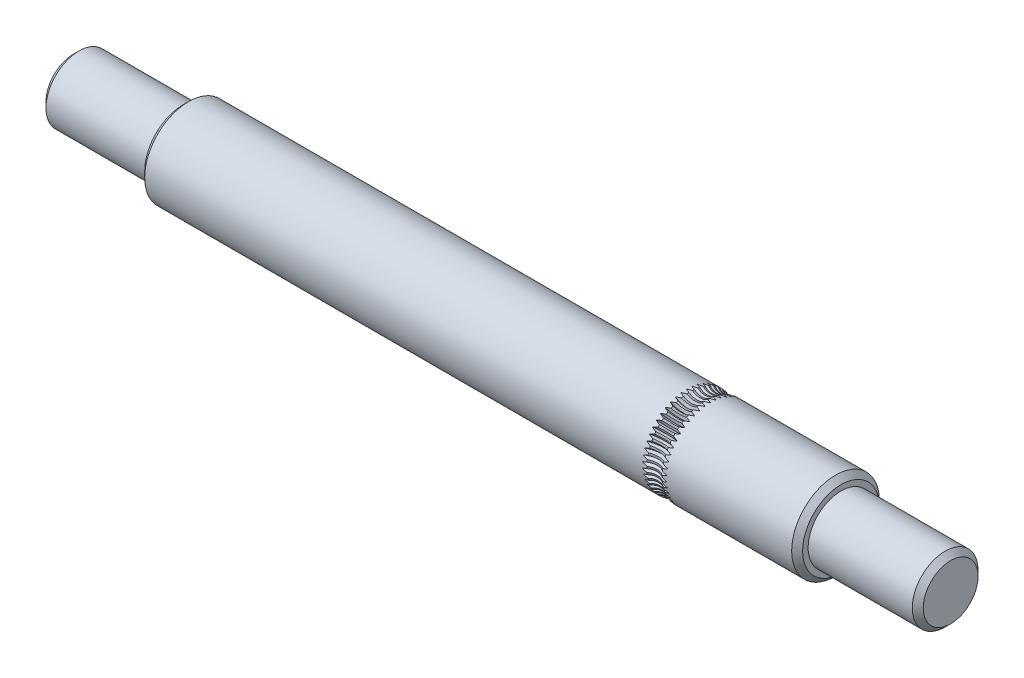
SolidWorks part; units mm, degrees
material "Plain Carbon Steel"
ref_plane "Front Plane" through (0, 0, 0) normal (0, 0, 1) x (1, 0, 0)
ref_plane "Top Plane" through (0, 0, 0) normal (0, 1, 0) x (1, 0, 0)
ref_plane "Right Plane" through (0, 0, 0) normal (1, 0, 0) x (0, 0, -1)
sketch "Sketch1" plane through (0, 0, 0) normal (0, 0, 1) x (1, 0, 0)
  line L0 (-47, 4) -> (13, 4)
  line L1 (-47, 3) -> (-57, 3)
  line L2 (-57, 0) -> (23, 0)
  line L3 (-47, 3) -> (-47, 4)
  line L4 (-57, 3) -> (-57, 0)
  line L5 (23, 0) -> (23, 3)
  line L6 (13, 4) -> (13, 3)
  line L7 (13, 3) -> (23, 3)
  line L8 (0, 0) -> (67.2135, 0) construction
  line L9 (0, 0) -> (0, 19.6593) construction
  dimension "D1" = 8
  dimension "D2" = 60
  dimension "D3" = 13
  dimension "D4" = 10
  dimension "D5" = 6
  dimension "D6" = 10
revolve "Revolve1" add sketch "Sketch1" angle 360 about L8
chamfer "Chamfer1" distance 0.5 angle 45 4 edges at (23, 0, 3) (13, 0, 4) (-47, 0, 4) (-57, 0, 3)
sketch "Sketch2" plane through (0, 0, 0) normal (1, 0, 0) x (0, 0, -1)
  line L0 (0, 0) -> (0, 5) construction
  line L1 (9.9899, 5) -> (-9.864, 5) construction
  line L2 (0.1562, 3.7705) -> (0, 3.5)
  line L3 (0, 3.5) -> (-0.1562, 3.7705)
  line L4 (-1.3354, 5) -> (1.3354, 5)
  line L5 (-0.1562, 3.7705) -> (-1.3354, 3.7705)
  line L6 (0.1562, 3.7705) -> (1.3354, 3.7705)
  line L7 (1.3354, 3.7705) -> (1.3354, 5)
  line L8 (-1.3354, 3.7705) -> (-1.3354, 5)
  line L9 (0, 0) -> (-6.9817, 0) construction
  line L10 (5.645, 4) -> (-5.97, 4) construction
  circle A0 centre (0, 0) radius 4 construction
  circle A1 centre (0, 0) radius 3.5 construction
  dimension "D5" = 5
  dimension "D1" = 60
  dimension "D2" = 3
  dimension "D3" = 2.459
  dimension "D4" = 1
revolve "Cut-Revolve1" cut sketch "Sketch2" angle 360 about L1
pattern_circular "CirPattern1" count 50 over 360 about axis through (0, 0, 0) along (-1, 0, 0) of "Cut-Revolve1"
sketch "Sketch3" plane through (0, 0, 0) normal (0, 0, 1) x (1, 0, 0)
  line L0 (22.5, 3) -> (13, 3) construction
  line L1 (8, 4) -> (0.75, 4)
  line L2 (8, 4) -> (8, 3)
  line L3 (8, 3) -> (0.75, 3)
  line L4 (0.75, 4) -> (0.75, 3)
  line L5 (-0.75, 4) -> (-8, 4)
  line L6 (-0.75, 4) -> (-0.75, 3)
  line L7 (-0.75, 3) -> (-8, 3)
  line L8 (-8, 4) -> (-8, 3)
  line L9 (0, 0) -> (0, 15.3026) construction
  line L10 (0, 0) -> (-13.7134, 0) construction
  line L11 (12.5, 4) -> (1.118, 4) construction
  dimension "D1" = 1.5
  dimension "D2" = 16
revolve "Cut-Revolve2" [suppressed] cut sketch "Sketch3" angle 360 about L10
